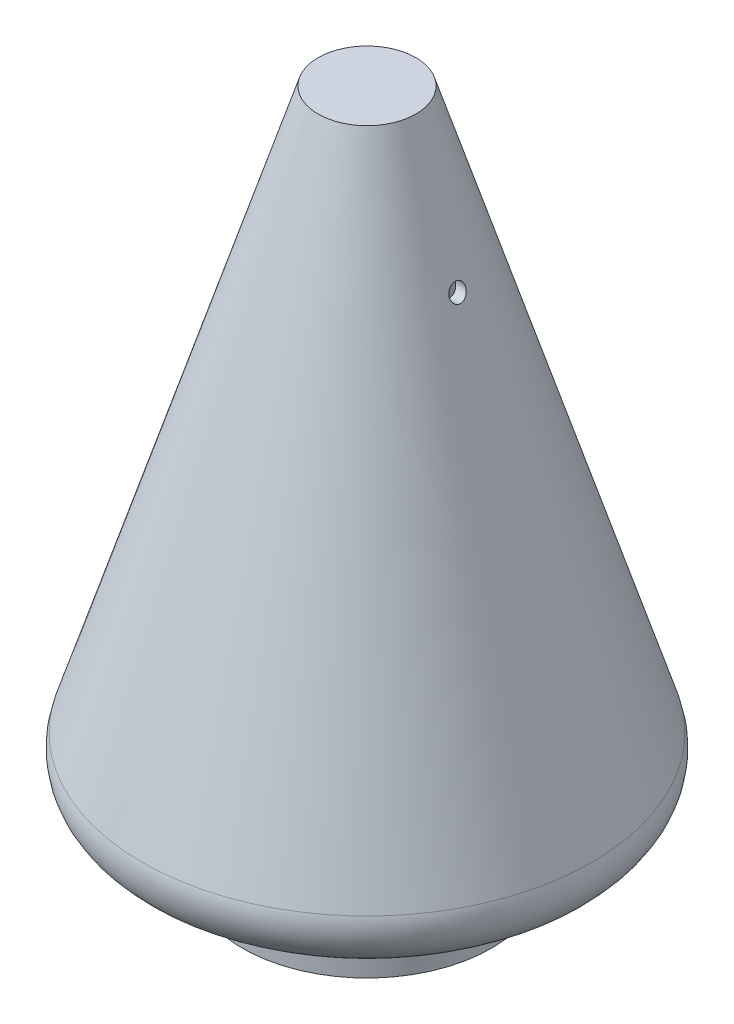
SolidWorks part; units mm, degrees
ref_plane "Plano frontal" through (0, 0, 0) normal (0, 0, 1) x (1, 0, 0)
ref_plane "Plano superior" through (0, 0, 0) normal (0, 1, 0) x (1, 0, 0)
ref_plane "Plano direito" through (0, 0, 0) normal (1, 0, 0) x (0, 0, -1)
sketch "Esboço1" plane through (0, 0, 0) normal (0, 0, 1) x (1, 0, 0)
  line L0 (0, 0) -> (0, 200) construction
  line L2 (67.5, 0) -> (67.5, 25) construction
  line L3 (0, 0) -> (10, 0)
  line L4 (10, 0) -> (34.5, 10.6522)
  line L5 (0, 200) -> (12.5, 200) construction
  line L6 (12.5, 200) -> (64.8028, 33.5821)
  line L7 (0, 200) -> (12.5, 200)
  line L8 (0, 0) -> (10, 0) construction
  line L9 (0, 200) -> (37.5, 200) construction
  line L10 (37.5, 200) -> (37.5, 11.9565) construction
  line L11 (37.5, 11.9565) -> (37.5, 86.9565)
  line L12 (0, 200) -> (0, 197)
  line L13 (14.7018, 203) -> (0, 203)
  line L14 (0, 203) -> (0, 200)
  line L15 (14.7018, 203) -> (67.6648, 34.4815)
  line L17 (0, -3) -> (10.624, -3)
  line L18 (34.5, 10.6522) -> (34.5, 86.9565)
  line L19 (34.5, 11.9565) -> (34.5, 86.9565) construction
  line L20 (37.5, 11.9565) -> (59.2501, 21.4131)
  line L21 (10, 0) -> (59.2501, 21.4131) construction
  line L22 (34.5, 86.9565) -> (37.5, 86.9565)
  line L23 (0, -3) -> (0, 0)
  line L24 (-3, 203) -> (-3, 197) construction
  line L25 (-3, 203) -> (14.7018, 203) construction
  line L26 (10.624, -3) -> (37.5, -3)
  line L27 (37.5, -3) -> (37.5, 8.6852)
  line L28 (37.5, 8.6852) -> (60.4463, 18.6619)
  line L29 (10.624, -3) -> (60.4463, 18.6619) construction
  arc A0 (59.2501, 21.4131) -> (64.8028, 33.5821) centre (55.2628, 30.5838) ccw
  arc A1 (60.4463, 18.6619) -> (67.6648, 34.4815) centre (55.2628, 30.5838) ccw
  dimension "D6" = 10
  dimension "D1" = 200
  dimension "D2" = 67.5
  dimension "D3" = 25
  dimension "D4" = 10
  dimension "D5" = 12.5
  dimension "D7" = 37.5
  dimension "D8" = 75
  dimension "D9" = 3
  dimension "D10" = 3
revolve "Revolução1" add sketch "Esboço1" angle 360 about L0
sketch "Esboço2" plane through (0, -3, 0) normal (0, -1, 0) x (1, 0, 0)
  circle A0 centre (0, 0) radius 2.5
  dimension "D1" = 5
extrude "Corte-extrusão1" cut sketch "Esboço2" against normal up to next
sketch "Esboço4" plane through (0, 0, 0) normal (1, 0, 0) x (0, 0, -1)
  circle A0 centre (0, 162.8192) radius 2.5
  dimension "D1" = 5
extrude "Corte-extrusão2" cut sketch "Esboço4" along normal blind 50
sketch "Esboço5" plane through (0, 0, 0) normal (0, 0, 1) x (1, 0, 0)
  circle A0 centre (0, 57.1869) radius 2.5
  dimension "D1" = 5
extrude "Corte-extrusão3" cut sketch "Esboço5" against normal blind 110
